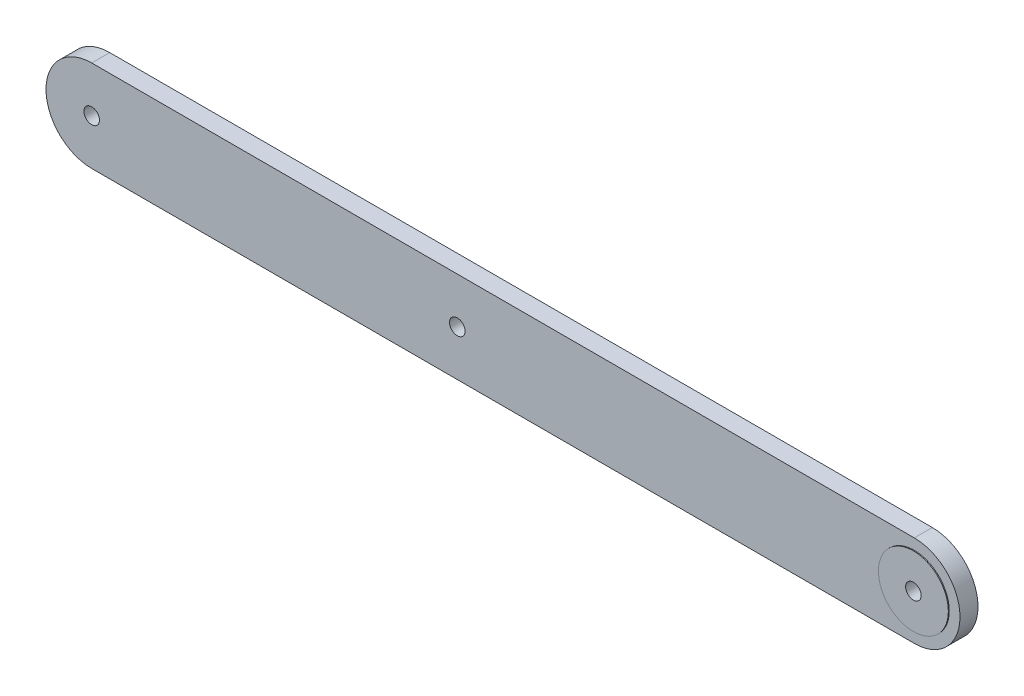
SolidWorks part; units mm, degrees
ref_plane "Front Plane" through (0, 0, 0) normal (0, 0, 1) x (1, 0, 0)
ref_plane "Top Plane" through (0, 0, 0) normal (0, 1, 0) x (1, 0, 0)
ref_plane "Right Plane" through (0, 0, 0) normal (1, 0, 0) x (0, 0, -1)
sketch "Sketch1" plane through (0, 0, 0) normal (0, 0, 1) x (1, 0, 0)
  line L1 (-101.6, 12.7) -> (127, 12.7)
  line L2 (-101.6, 12.7) -> (-101.6, -12.7)
  line L3 (-101.6, -12.7) -> (127, -12.7)
  line L4 (127, 12.7) -> (127, -12.7)
  circle A0 centre (0, 0) radius 6.223
  circle A1 centre (127, 0) radius 6.35
  circle A2 centre (-101.6, 0) radius 2.159
  arc A3 (127, -12.7) -> (127, 12.7) centre (127, 0) ccw
  arc A4 (-101.6, -12.7) -> (-101.6, 12.7) centre (-101.6, 0) cw
  point P11 (-101.6, 0)
  point P12 (127, 0)
  dimension "D3" = 12.446
  dimension "D4" = 12.7
  dimension "D5" = 4.318
  dimension "D1" = 101.6
  dimension "D2" = 127
  dimension "D6" = 0
  dimension "D7" = 0
  dimension "D8" = 25.4
  dimension "D9" = 12.7
extrude "Boss-Extrude1" add sketch "Sketch1" along normal blind 5.0038 contours A2 L2 L3 L4 A1 L1 A0 | A0 | L4 A3 A1 | A4 L2 A2
sketch "Sketch2" plane through (0, 0, 5.0038) normal (0, 0, 1) x (1, 0, 0)
  circle A0 centre (0, 0) radius 2.159
  dimension "D1" = 4.318
sketch "Sketch6" plane through (0, 0, 5.0038) normal (0, 0, 1) x (1, 0, 0)
  circle A0 centre (127, 0) radius 9.7158
  circle A1 centre (127, 0) radius 2.159
  dimension "D1" = 4.318
extrude "Boss-Extrude3" add sketch "Sketch6" against normal blind 5.0038 and the other way blind 0.254
extrude "Cut-Extrude1" cut sketch "Sketch2" against normal blind 19.812 contours A0
